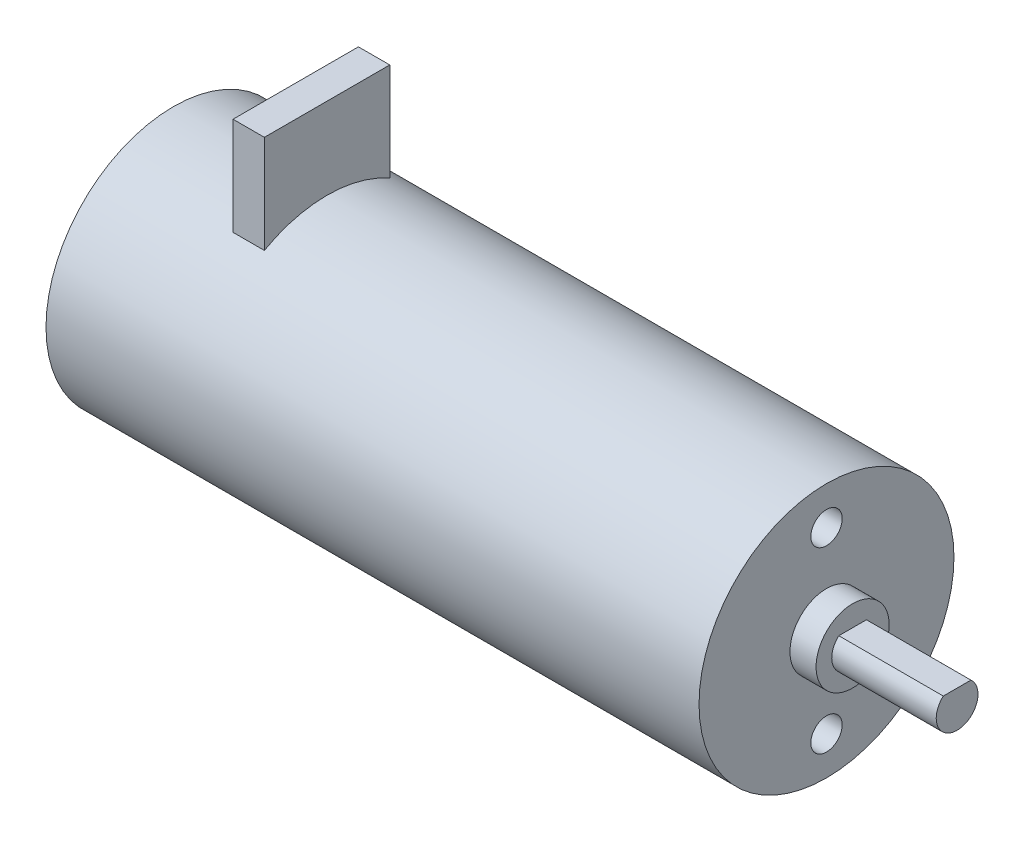
SolidWorks part; units mm, degrees
ref_plane "Front Plane" through (0, 0, 0) normal (0, 0, 1) x (1, 0, 0)
ref_plane "Top Plane" through (0, 0, 0) normal (0, 1, 0) x (1, 0, 0)
ref_plane "Right Plane" through (0, 0, 0) normal (1, 0, 0) x (0, 0, -1)
sketch "Sketch1" plane through (0, 0, 0) normal (1, 0, 0) x (0, 0, -1)
  circle A0 centre (0, 0) radius 12.2
  dimension "D1" = 24.4
extrude "Boss-Extrude1" add sketch "Sketch1" along normal blind 62.5
sketch "Sketch2" plane through (62.5, 0, 0) normal (1, 0, 0) x (0, 0, -1)
  circle A0 centre (0, 0) radius 3.5
  dimension "D1" = 7
extrude "Boss-Extrude2" add sketch "Sketch2" along normal blind 2.5
sketch "Sketch3" plane through (65, 0, 0) normal (1, 0, 0) x (0, 0, -1)
  line L0 (-1.3229, 1.5) -> (1.3229, 1.5)
  arc A0 (-1.3229, 1.5) -> (1.3229, 1.5) centre (0, 0) ccw
  dimension "D1" = 4
  dimension "D2" = 1.5
extrude "Boss-Extrude3" add sketch "Sketch3" along normal blind 10
sketch "Sketch4" plane through (62.5, 0, 0) normal (1, 0, 0) x (0, 0, -1)
  line L0 (0, 0) -> (13.2707, 0) construction
  circle A0 centre (0, 8.55) radius 1.5
  circle A1 centre (0, -8.55) radius 1.5
  dimension "D1" = 3
  dimension "D2" = 8.55
extrude "Cut-Extrude1" cut sketch "Sketch4" against normal blind 5
sketch "Sketch5" plane through (0, 0, 0) normal (0, 1, 0) x (1, 0, 0)
  line L0 (0, 12.2) -> (0, -12.2) construction
  line L1 (11.7, 6) -> (14.7, 6)
  line L2 (11.7, 6) -> (11.7, -6)
  line L3 (11.7, -6) -> (14.7, -6)
  line L4 (14.7, 6) -> (14.7, -6)
  dimension "D1" = 14.7
  dimension "D2" = 6
  dimension "D3" = 6
  dimension "D4" = 3
extrude "Boss-Extrude4" add sketch "Sketch5" along normal blind 20
equation "\"D1@Boss-Extrude1\"=17+30.8+14.7"
